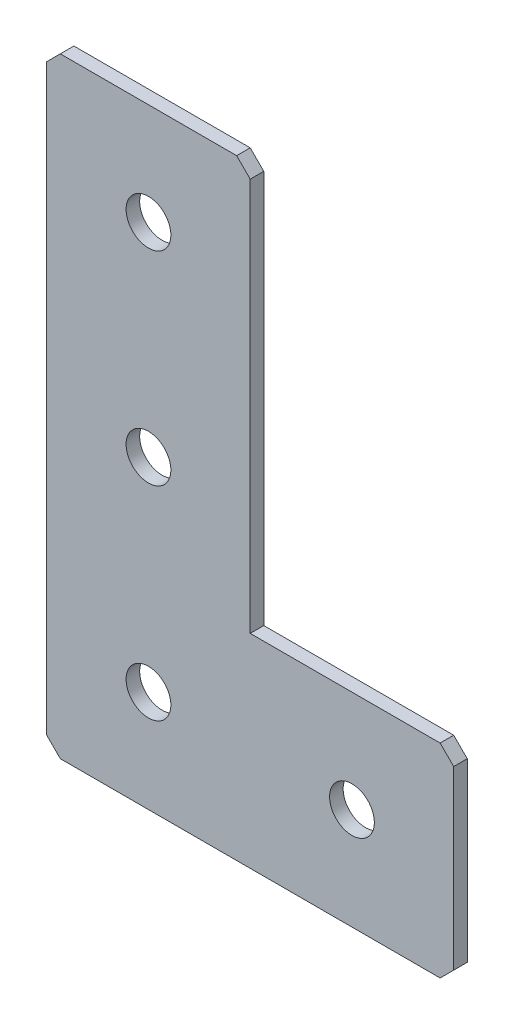
SolidWorks part; units mm, degrees
material "Простая углеродистая сталь"
ref_plane "Спереди(Плоскость XY)" through (0, 0, 0) normal (0, 0, 1) x (1, 0, 0)
ref_plane "Сверху(Плоскость XZ)" through (0, 0, 0) normal (0, 1, 0) x (1, 0, 0)
ref_plane "Справа(Плоскость ZY)" through (0, 0, 0) normal (1, 0, 0) x (0, 0, -1)
sketch "Эскиз1" plane through (0, 0, 0) normal (0, 0, -1) x (1, 0, 0)
  line L0 (0, 0) -> (0, 90)
  line L1 (0, 90) -> (60, 90)
  line L2 (60, 90) -> (60, 60)
  line L3 (60, 60) -> (30, 60)
  line L4 (30, 60) -> (30, 0)
  line L5 (30, 0) -> (0, 0)
  dimension "D1" = 90
  dimension "D2" = 30
  dimension "D3" = 30
  dimension "D4" = 30
extrude "Бобышка-Вытянуть1" add sketch "Эскиз1" along normal blind 2
hole_wizard "Отверстие с зазором M61" positions "Эскиз2" profile "Эскиз3" hole size "M6" standard "DIN" end condition through all
sketch "Эскиз2" plane through (0, 0, -2) normal (0, 0, -1) x (1, 0, 0)
  line L1 (0, 0) -> (30, 0) construction
  line L6 (0, 90) -> (0, 0) construction
  point P0 (45, 75)
  point P2 (15, 75)
  point P4 (15, 45)
  point P6 (15, 15)
  dimension "D1" = 30
  dimension "D2" = 30
  dimension "D3" = 30
  dimension "D4" = 15
  dimension "D5" = 15
sketch "Эскиз3" plane through (45, -75, -2) normal (1, 0, 0) x (0, 1, 0)
  line L0 (0, 0) -> (0, 2)
  line L1 (0, 2) -> (3.3, 2)
  line L2 (3.3, 2) -> (3.3, 0)
  line L5 (3.3, 0) -> (0, 0)
  line L11 (0, -6.35) -> (0, 107.95) construction
  dimension "Диаметр сквозного отверстия" = 6.6
  dimension "Глубина сквозного отверстия" = 2
chamfer "Фаска1" distance 2 angle 45 5 edges at (0, 0, -1) (30, 0, -1) (60, -60, -1) (60, -90, -1) (0, -90, -1)
